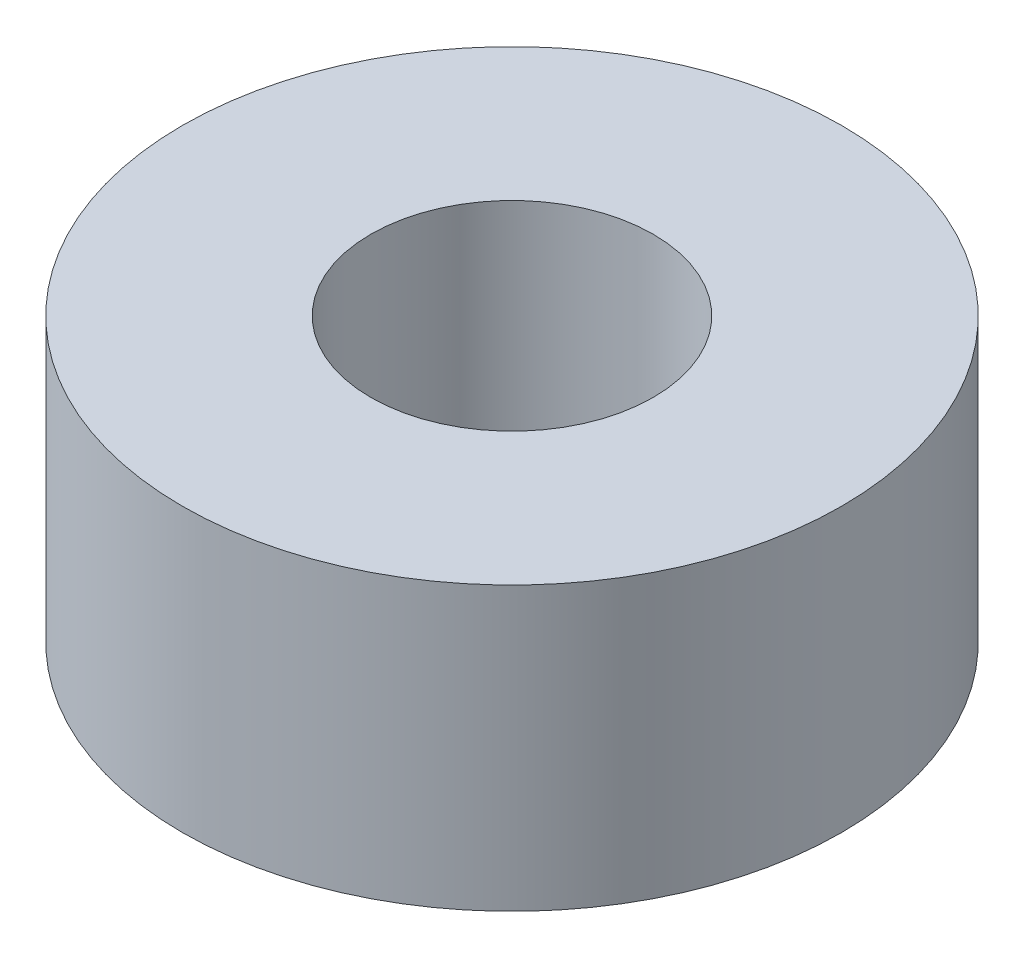
SolidWorks part; units mm, degrees
ref_plane "Front Plane" through (0, 0, 0) normal (0, 0, 1) x (1, 0, 0)
ref_plane "Top Plane" through (0, 0, 0) normal (0, 1, 0) x (1, 0, 0)
ref_plane "Right Plane" through (0, 0, 0) normal (1, 0, 0) x (0, 0, -1)
sketch "Sketch1" plane through (0, 0, 0) normal (0, 1, 0) x (1, 0, 0)
  circle A0 centre (0, 0) radius 3.5
  circle A1 centre (0, 0) radius 1.5
  dimension "D1" = 7
  dimension "D2" = 3
extrude "Boss-Extrude1" add sketch "Sketch1" along normal blind 3
